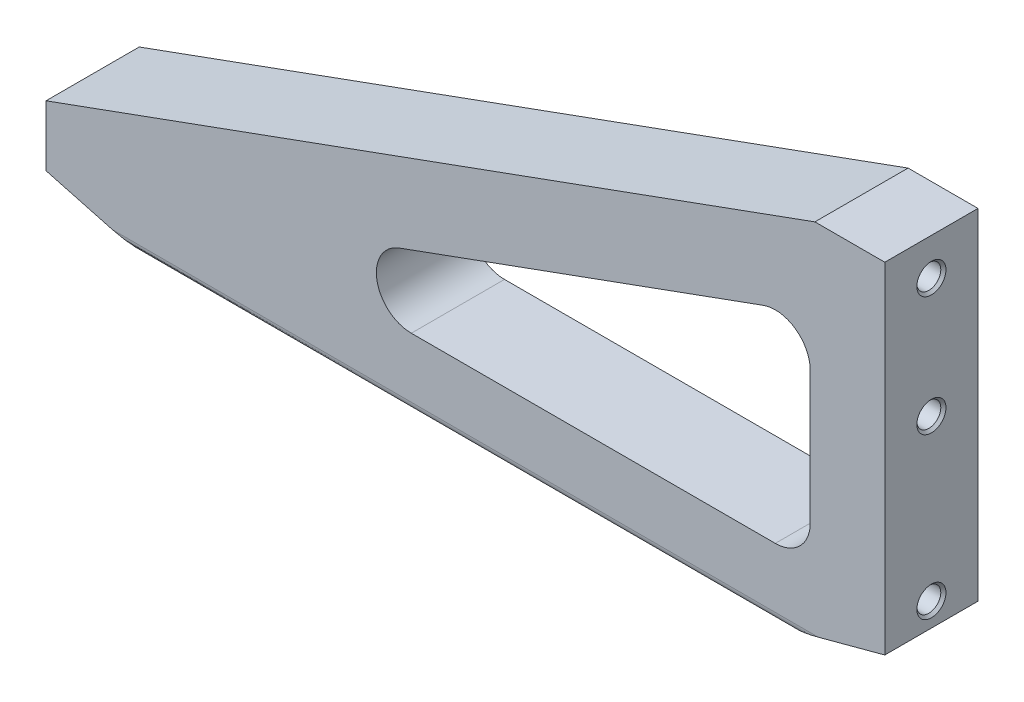
SolidWorks part; units mm, degrees
material "6061-T6 Al"
ref_plane "Front" through (0, 0, 0) normal (0, 0, 1) x (1, 0, 0)
ref_plane "Top" through (0, 0, 0) normal (0, 1, 0) x (1, 0, 0)
ref_plane "Right" through (0, 0, 0) normal (1, 0, 0) x (0, 0, -1)
sketch "Sketch1 w/mock PCB" plane through (0, 0, 0) normal (0, 0, 1) x (1, 0, 0)
  line L0 (-151.5904, 0) -> (0, 0) construction
  line L1 (-19.05, 48.1965) -> (-228.6, -28.0035)
  line L2 (-19.05, 48.1965) -> (0, 48.1965)
  line L3 (-228.6, -28.0035) -> (-228.6, -44.5135)
  line L4 (-195.4221, -53.4035) -> (-33.1779, -53.4035)
  line L6 (0, 48.1965) -> (0, -44.5135)
  line L7 (-20.32, 12.5141) -> (-20.32, -23.5585)
  line L8 (-129.0446, -33.0835) -> (-29.845, -33.0835)
  line L9 (-33.1001, 21.4656) -> (-132.2997, -14.607)
  line L10 (-20.32, 48.1965) -> (-20.32, -33.0835) construction
  line L11 (-152.4, -33.0835) -> (-20.32, -33.0835) construction
  line L12 (-12.1058, 29.0999) -> (-221.6558, -47.1001) construction
  line L13 (-152.4, -53.4035) -> (0, -53.4035) construction
  line L17 (-228.6, -44.5135) -> (-195.4221, -53.4035)
  line L18 (0, 48.1965) -> (0, -53.4035) construction
  line L19 (-33.1779, -53.4035) -> (0, -44.5135)
  arc A0 (-20.32, -23.5585) -> (-29.845, -33.0835) centre (-29.845, -23.5585) cw
  arc A2 (-129.0446, -33.0835) -> (-132.2997, -14.607) centre (-129.0446, -23.5585) cw
  arc A3 (-33.1001, 21.4656) -> (-20.32, 12.5141) centre (-29.845, 12.5141) cw
  point P5 (-25.908, 20.828)
  point P6 (25.908, 20.828)
  point P7 (25.908, -20.828)
  point P8 (-25.908, -20.828)
  point P63 (-25.781, -19.05)
  point P64 (25.781, -19.05)
  dimension "D5" = 20.32
  dimension "D6" = 20.32
  dimension "D7" = 9.525
  dimension "D8" = 25.4
  dimension "D9" = 75
  dimension "D10" = 75
  dimension "D1" = 228.6
  dimension "D2" = 101.6
  dimension "D3" = 19.05
  dimension "D4" = 48.1965
  dimension "D11" = 8.89
extrude "Boss-Extrude1" add sketch "Sketch1 w/mock PCB" along normal mid plane 25.4
hole_wizard "5/16-18 Tapped Hole1" positions "Sketch7" profile "Sketch6" tap size "5/16-18" standard "ANSI Inch"
sketch "Sketch7" plane through (0, 31.3935, 0.7652) normal (-1, 0, 0) x (0, 0, 1)
  line L5 (-0.7652, 6.7065) -> (-0.7652, -69.4935) construction
  point P0 (-0.7652, -69.4935)
  point P2 (-0.7652, -25.8563)
  point P5 (-0.7652, 6.7065)
  dimension "D1" = 76.2
  dimension "D2" = 32.5628
sketch "Sketch6" plane through (0, -38.1, 0) normal (0, 1, 0) x (0, 0, -1)
  line L0 (0, 0) -> (0, 22.0779)
  line L1 (0, 22.0779) -> (3.2639, 20.1168)
  line L2 (3.2639, 20.1168) -> (3.2639, 0.7048)
  line L3 (3.2639, 0.7048) -> (3.9688, 0)
  line L5 (3.9688, 0) -> (0, 0)
  line L6 (-3.2639, 0.7048) -> (-3.9688, 0) construction
  line L10 (0, 22.0779) -> (-3.2639, 20.1168) construction
  line L11 (0, -6.35) -> (0, 107.95) construction
  dimension "Tap Drill Dia." = 6.5278
  dimension "Tap Drill Depth" = 20.1168
  dimension "Near C'Sink Dia." = 7.9375
  dimension "Near C'Sink Angle" = 90
  dimension "Drill Angle" = 118
cosmetic thread "Hole Thread1" parameters "D1"=15.875, "D2"=7.9375
cosmetic thread "Hole Thread2" parameters "D1"=15.875, "D2"=7.9375
cosmetic thread "Hole Thread3" parameters "D1"=15.875, "D2"=7.9375
sketch "Sketch8" plane through (0, 0, 0) normal (1, 0, 0) x (0, 0, -1)
  line L0 (0, 55.0069) -> (0, -55.0069) construction
  line L2 (-12.7, 48.1965) -> (12.7, 48.1965) construction
  line L3 (-12.7, -53.4035) -> (12.7, -53.4035) construction
  line L4 (12.7, -44.5135) -> (12.7, 48.1965)
  line L5 (12.7, 48.1965) -> (-12.7, 48.1965)
  line L6 (-12.7, 48.1965) -> (-12.7, -44.5135)
  line L7 (-12.7, -44.5135) -> (12.7, -44.5135)
  line L8 (12.7, 48.1965) -> (12.7, -51.7253)
  line L10 (-12.7, -51.7253) -> (-12.7, 48.1965)
  line L11 (-12.7, 48.1965) -> (12.7, 48.1965)
  arc A0 (-12.7, -51.7253) -> (12.7, -51.7253) centre (0, 837.184) ccw
  dimension "D2" = 889
  dimension "D3" = 1.5875
  dimension "D1" = 0
extrude "Cut-Extrude1" cut sketch "Sketch8" against normal through all flip side to cut
fillet "Fillet1" radius 2.3813 2 edges at (-114.3, -51.7253, -12.7) (-114.3, -51.7253, 12.7)
